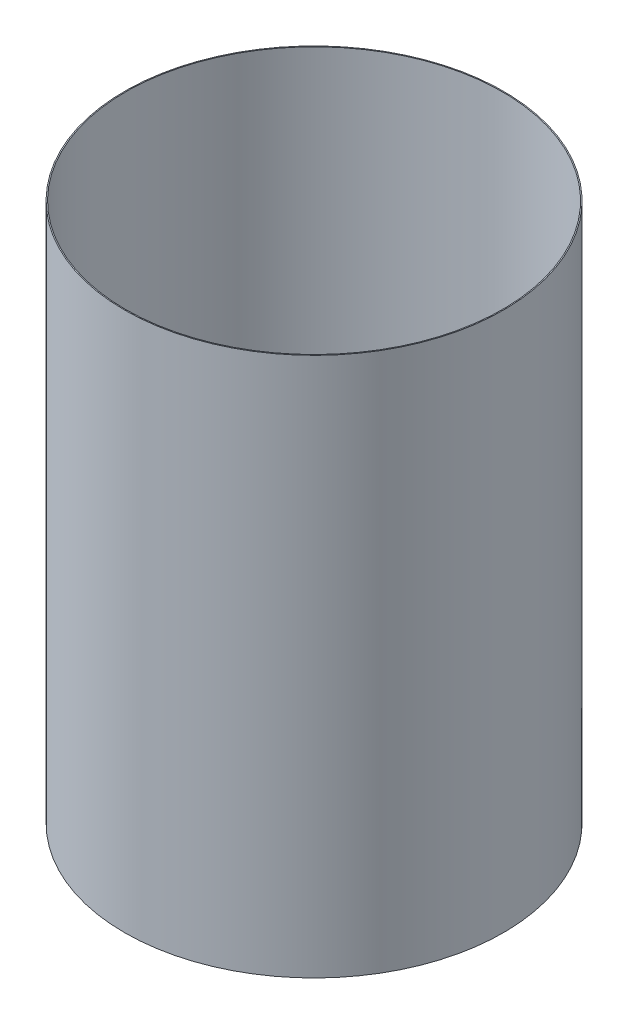
SolidWorks part; units mm, degrees
material "Thornel Mat VMA"
ref_plane "Front Plane" through (0, 0, 0) normal (0, 0, 1) x (1, 0, 0)
ref_plane "Top Plane" through (0, 0, 0) normal (0, 1, 0) x (1, 0, 0)
ref_plane "Right Plane" through (0, 0, 0) normal (1, 0, 0) x (0, 0, -1)
ref_axis "Axis1" through (0, 55, 0) along (0, -1, 0)
sketch "Sketch1" plane through (0, 0, 0) normal (0, 0, 1) x (1, 0, 0)
  line L0 (-46.609, -19.9059) -> (-46.609, -153.2559)
  line L2 (-38.1, -19.9059) -> (0, -19.9059) construction
  line L3 (-38.1, -153.2559) -> (0, -153.2559) construction
revolve "Revolve-Thin1" add sketch "Sketch1" angle 360 about axis through (0, 55, 0) along (0, -1, 0)
equation "\"D3@Revolve-Thin1\"=\"CF THICKNESS@Cryo Tank.SLDASM\""
